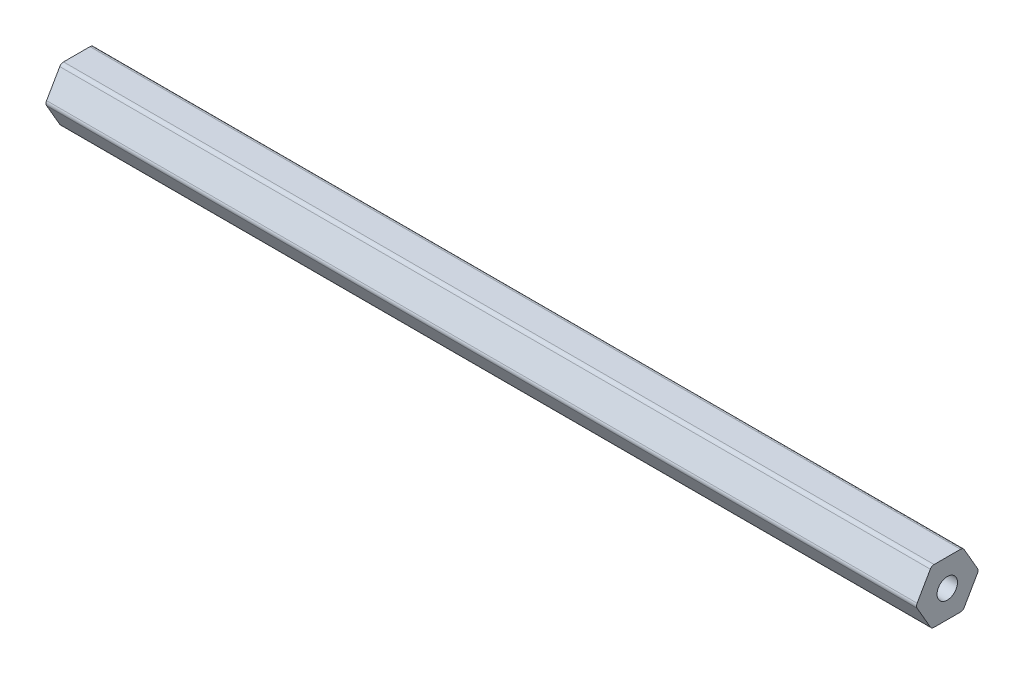
SolidWorks part; units mm, degrees
material "7075-T6 (SN)"
ref_plane "Front Plane" through (0, 0, 0) normal (0, 0, 1) x (1, 0, 0)
ref_plane "Top Plane" through (0, 0, 0) normal (0, 1, 0) x (1, 0, 0)
ref_plane "Right Plane" through (0, 0, 0) normal (1, 0, 0) x (0, 0, -1)
sketch "Sketch1" plane through (0, 0, 0) normal (1, 0, 0) x (0, 0, -1)
  line L1 (7.0391, 0.508) -> (3.9595, 5.842)
  line L2 (3.0796, 6.35) -> (-3.0796, 6.35)
  line L3 (-3.9595, 5.842) -> (-7.0391, 0.508)
  line L4 (-7.0391, -0.508) -> (-3.9595, -5.842)
  line L5 (-3.0796, -6.35) -> (3.0796, -6.35)
  line L6 (3.9595, -5.842) -> (7.0391, -0.508)
  circle A0 centre (0, 0) radius 6.35 construction
  arc A1 (3.0796, 6.35) -> (3.9595, 5.842) centre (3.0796, 5.334) cw
  arc A2 (7.0391, 0.508) -> (7.0391, -0.508) centre (6.1592, 0) cw
  arc A3 (3.9595, -5.842) -> (3.0796, -6.35) centre (3.0796, -5.334) cw
  arc A4 (-3.0796, -6.35) -> (-3.9595, -5.842) centre (-3.0796, -5.334) cw
  arc A5 (-7.0391, -0.508) -> (-7.0391, 0.508) centre (-6.1592, 0) cw
  arc A6 (-3.9595, 5.842) -> (-3.0796, 6.35) centre (-3.0796, 5.334) cw
  circle A7 centre (0, 0) radius 2.3813
  point P11 (3.6662, 6.35)
  point P14 (7.3323, 0)
  dimension "D1" = 12.7
  dimension "D3" = 1.016
  dimension "D4" = 4.7625
  dimension "D2" = 6.35
extrude "Boss-Extrude1" add sketch "Sketch1" along normal blind 203.2
